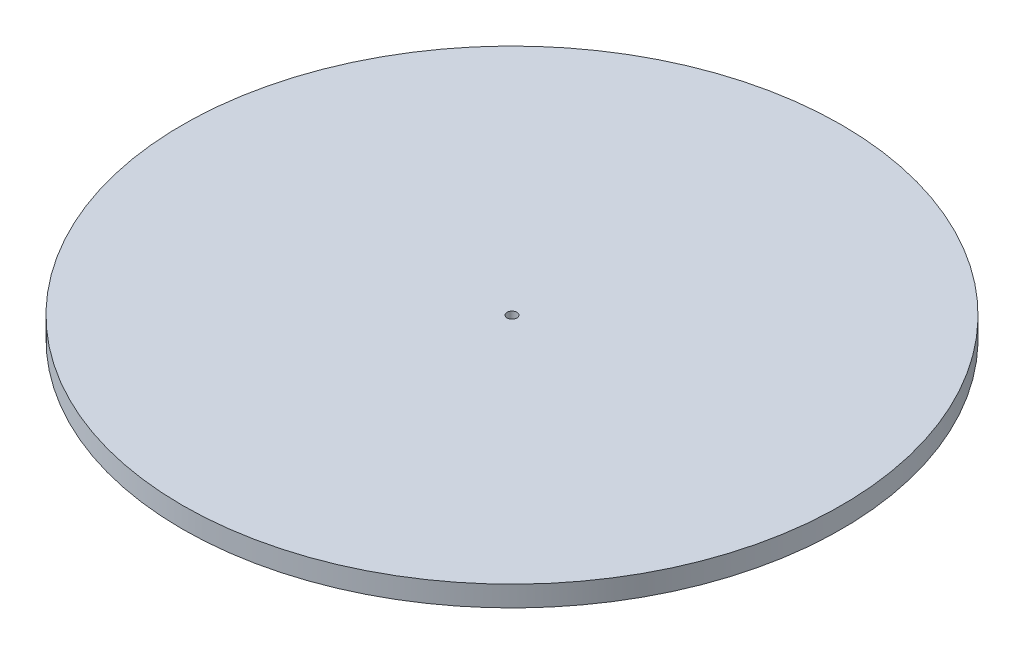
SolidWorks part; units mm, degrees
ref_plane "Front Plane" through (0, 0, 0) normal (0, 0, 1) x (1, 0, 0)
ref_plane "Top Plane" through (0, 0, 0) normal (0, 1, 0) x (1, 0, 0)
ref_plane "Right Plane" through (0, 0, 0) normal (1, 0, 0) x (0, 0, -1)
sketch "Sketch1" plane through (0, 0, 0) normal (0, 1, 0) x (1, 0, 0)
  circle A0 centre (0, 0) radius 50.8
  circle A1 centre (0, 0) radius 0.762
  dimension "D1" = 101.6
  dimension "D2" = 1.524
extrude "Boss-Extrude1" add sketch "Sketch1" against normal blind 3.175
